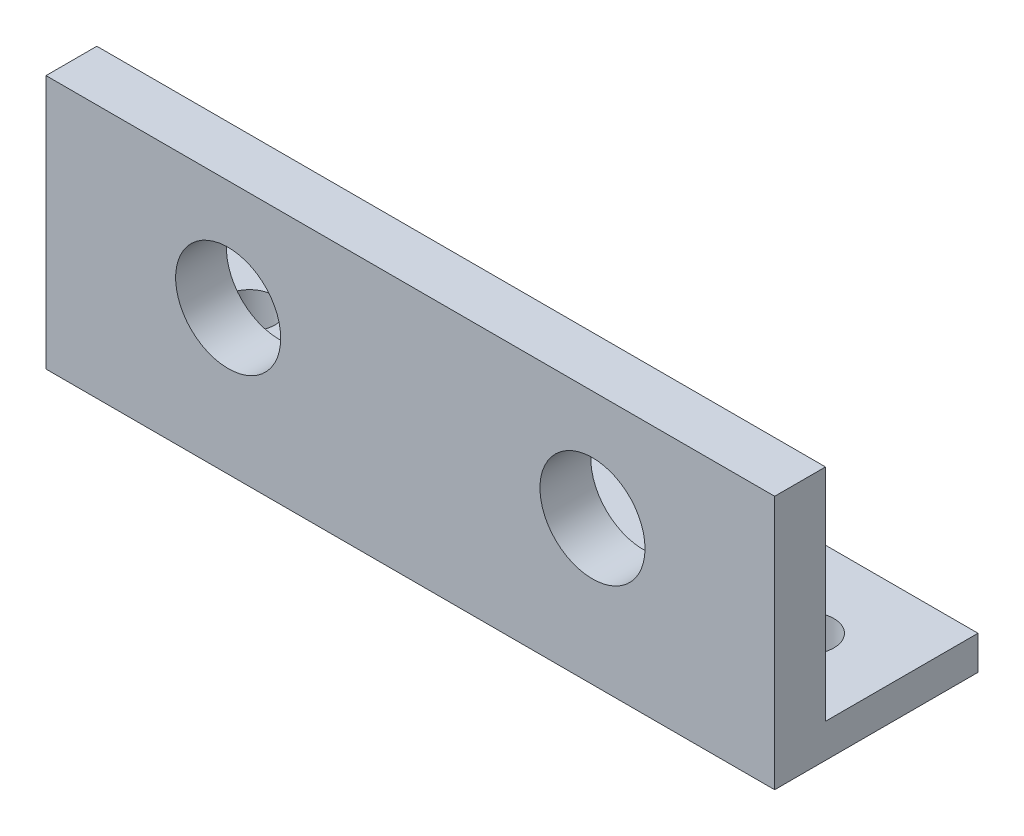
SolidWorks part; units mm, degrees
ref_plane "Front Plane" through (0, 0, 0) normal (0, 0, 1) x (1, 0, 0)
ref_plane "Top Plane" through (0, 0, 0) normal (0, 1, 0) x (1, 0, 0)
ref_plane "Right Plane" through (0, 0, 0) normal (1, 0, 0) x (0, 0, -1)
sketch "Sketch1" plane through (0, 0, 0) normal (0, 1, 0) x (1, 0, 0)
  line L0 (0, 0) -> (-33, 0)
  line L1 (0, 0) -> (5, 0)
  line L2 (5, 0) -> (5, 5)
  line L3 (-33, 0) -> (-38, 0)
  line L4 (-38, 0) -> (-38, 5)
  line L5 (-38, 5) -> (5, 5)
  line L6 (5, 0) -> (5, -4)
  line L7 (5, -4) -> (-38, -4)
  line L8 (-38, -4) -> (-38, 0)
  line L9 (5, -4) -> (5, -7)
  line L10 (5, -7) -> (-38, -7)
  line L11 (-38, -7) -> (-38, -4)
  circle A0 centre (0, 0) radius 1.5
  circle A1 centre (-33, 0) radius 1.5
extrude "Boss-Extrude1" add sketch "Sketch1" along normal blind 2 contours A1 L0 A0 L1 L2 L5 L4 L3 | A1 L3 L8 L7 L6 L1 A0 L0 | L11 L10 L9 L7
sketch "Sketch2" plane through (0, 2, 0) normal (0, 1, 0) x (1, 0, 0)
  line L0 (-38, -7) -> (-38, -4)
  line L1 (-38, -7) -> (-38, 5) construction
  line L2 (-38, -4) -> (5, -4)
  line L3 (5, -7) -> (5, 5) construction
  line L4 (5, -4) -> (5, -7)
  line L5 (5, -7) -> (-38, -7)
extrude "Boss-Extrude2" add sketch "Sketch2" along normal blind 13
sketch "Sketch3" plane through (0, 0, 7) normal (0, 0, 1) x (1, 0, 0)
  line L0 (5, 15) -> (-16.5, 15)
  line L2 (-38, 15) -> (5, 15) construction
  line L3 (-16.5, 15) -> (-5.75, 15)
  line L4 (-5.75, 15) -> (-5.75, 8.5)
  line L5 (-16.5, 15) -> (-38, 15)
  line L6 (-38, 15) -> (-27.25, 15)
  line L7 (-27.25, 15) -> (-27.25, 8.5)
  circle A0 centre (-27.25, 8.5) radius 3.1
  circle A1 centre (-5.75, 8.5) radius 3.1
extrude "Cut-Extrude1" cut sketch "Sketch3" against normal blind 13
